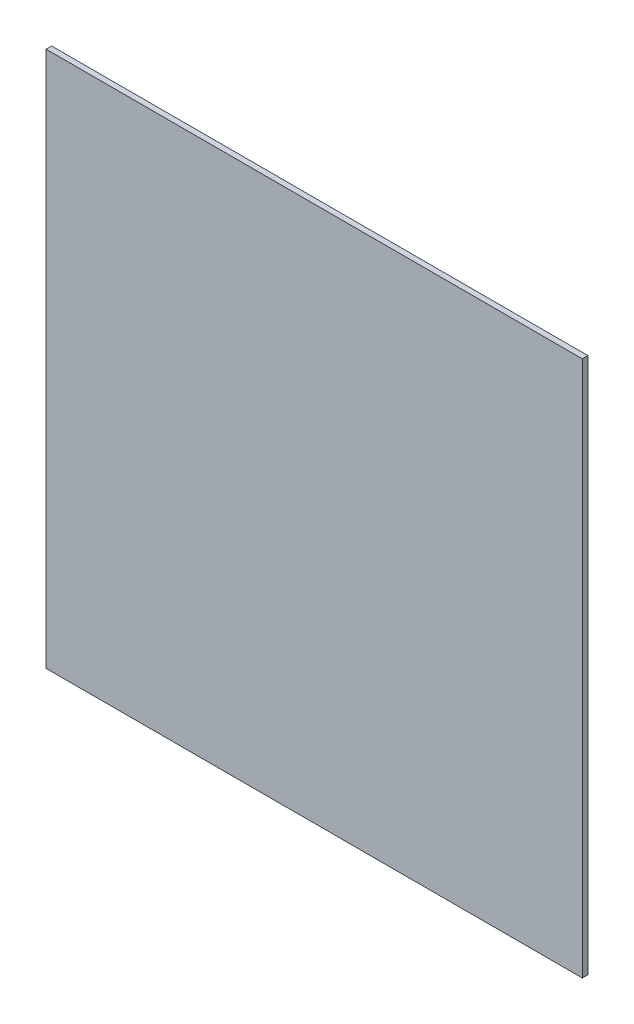
SolidWorks part; units mm, degrees
material "Plain Carbon Steel"
ref_plane "Front Plane" through (0, 0, 0) normal (0, 0, 1) x (1, 0, 0)
ref_plane "Top Plane" through (0, 0, 0) normal (0, 1, 0) x (1, 0, 0)
ref_plane "Right Plane" through (0, 0, 0) normal (1, 0, 0) x (0, 0, -1)
sketch "Sketch1" plane through (0, 0, 0) normal (0, 0, 1) x (1, 0, 0)
  line L1 (0, 0) -> (-609.6, 0)
  line L2 (0, 0) -> (0, 609.6)
  line L3 (0, 609.6) -> (-609.6, 609.6)
  line L4 (-609.6, 0) -> (-609.6, 609.6)
  dimension "D1" = 609.6
  dimension "D2" = 609.6
extrude "Boss-Extrude1" add sketch "Sketch1" along normal blind 6.35
